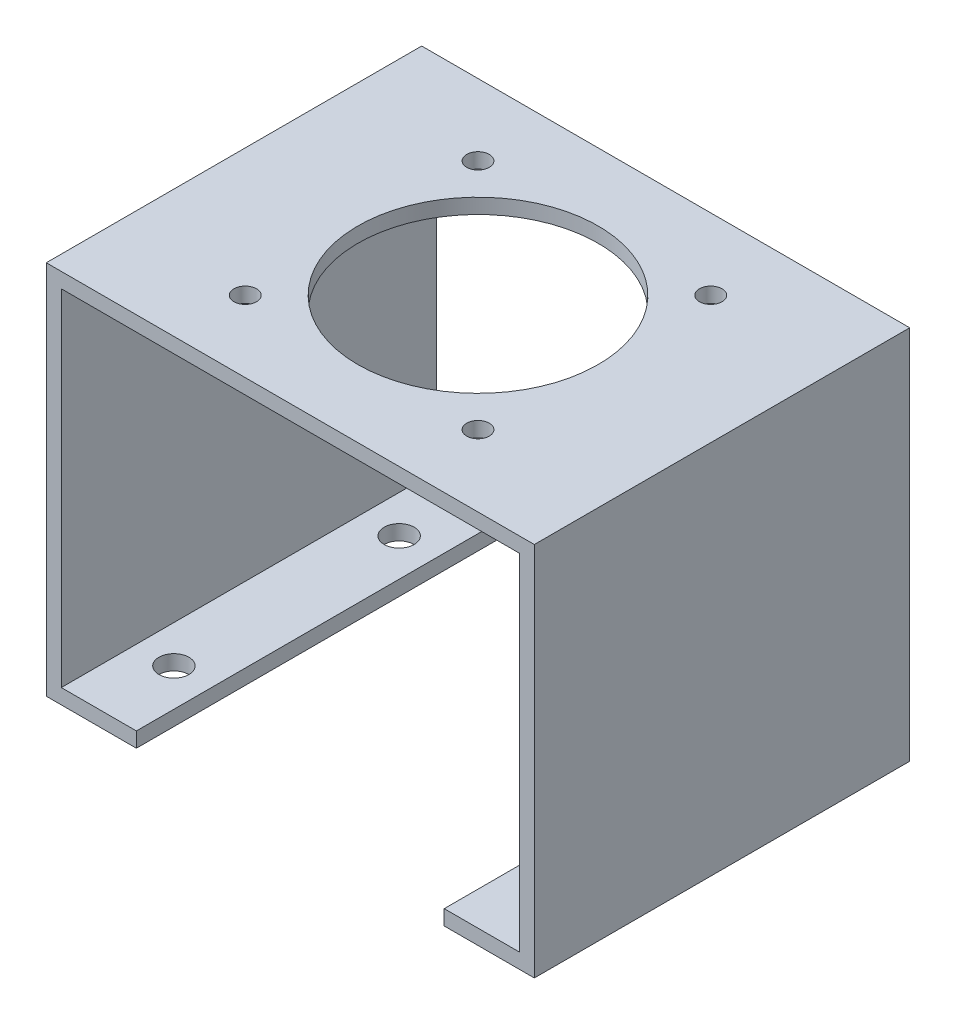
SolidWorks part; units mm, degrees
material "Liga 1060"
ref_plane "Plano frontal" through (0, 0, 0) normal (0, 0, 1) x (1, 0, 0)
ref_plane "Plano superior" through (0, 0, 0) normal (0, 1, 0) x (1, 0, 0)
ref_plane "Plano direito" through (0, 0, 0) normal (1, 0, 0) x (0, 0, -1)
sketch "Esboço1" plane through (0, 0, 0) normal (0, 1, 0) x (1, 0, 0)
  line L1 (32.5, -25) -> (-32.5, -25)
  line L2 (32.5, -25) -> (32.5, 25)
  line L3 (32.5, 25) -> (-32.5, 25)
  line L4 (-32.5, -25) -> (-32.5, 25)
  point P0 (0, 0)
  point P7 (0, -25)
  dimension "D1" = 65
  dimension "D2" = 50
extrude "Ressalto-extrusão1" add sketch "Esboço1" against normal blind 2
sketch "Esboço2" plane through (-32.5, 0, 0) normal (-1, 0, 0) x (0, 0, 1)
  line L0 (25, -2) -> (25, 0) construction
  line L1 (-25, 0) -> (25, 0)
  line L2 (-25, 0) -> (-25, -50)
  line L3 (-25, -50) -> (25, -50)
  line L4 (25, 0) -> (25, -50)
  dimension "D1" = 50
extrude "Ressalto-extrusão2" add sketch "Esboço2" against normal blind 2
sketch "Esboço3" plane through (-30.5, 0, 0) normal (1, 0, 0) x (0, 0, -1)
  line L0 (25, -2) -> (25, -50) construction
  line L1 (-25, -50) -> (25, -50)
  line L2 (-25, -50) -> (-25, -48)
  line L3 (-25, -48) -> (25, -48)
  line L4 (25, -50) -> (25, -48)
  dimension "D1" = 2
extrude "Ressalto-extrusão3" add sketch "Esboço3" along normal blind 10
mirror "Espelhar1" about plane through (0, 0, 0) normal (1, 0, 0) of "Ressalto-extrusão3", "Ressalto-extrusão2"
sketch "Esboço4" plane through (0, 0, 0) normal (0, 1, 0) x (1, 0, 0)
  circle A0 centre (-15.5, 15.5) radius 1.5 construction
  circle A1 centre (-15.5, -15.5) radius 1.5 construction
  circle A2 centre (15.5, -15.5) radius 1.5 construction
  circle A3 centre (15.5, 15.5) radius 1.5 construction
  circle A4 centre (-15.5, 15.5) radius 1.5
  circle A5 centre (-15.5, -15.5) radius 1.5
  circle A6 centre (15.5, -15.5) radius 1.5
  circle A7 centre (15.5, 15.5) radius 1.5
extrude "Corte-extrusão1" cut sketch "Esboço4" against normal through all
sketch "Esboço5" plane through (0, 0, 0) normal (0, 1, 0) x (1, 0, 0)
  circle A0 centre (0, 0) radius 2.5 construction
  circle A1 centre (0, 0) radius 2.5
  circle A2 centre (0, 0) radius 16
  dimension "D1" = 32
extrude "Corte-extrusão2" cut sketch "Esboço5" against normal blind 10 contours A2 A1 | A1
sketch "Esboço6" plane through (0, -48, 0) normal (0, 1, 0) x (1, 0, 0)
  line L0 (-30.5, 25) -> (-30.5, -25) construction
  line L1 (-20.5, -25) -> (-30.5, -25) construction
  line L2 (0, -27.5) -> (0, 27.5) construction
  line L3 (-27.5, 0) -> (27.5, 0) construction
  circle A0 centre (-25.5, -15) radius 2
  circle A1 centre (25.5, -15) radius 2
  circle A2 centre (25.5, 15) radius 2
  circle A3 centre (-25.5, 15) radius 2
  dimension "D1" = 4
  dimension "D2" = 5
  dimension "D3" = 10
extrude "Corte-extrusão3" cut sketch "Esboço6" against normal blind 10
